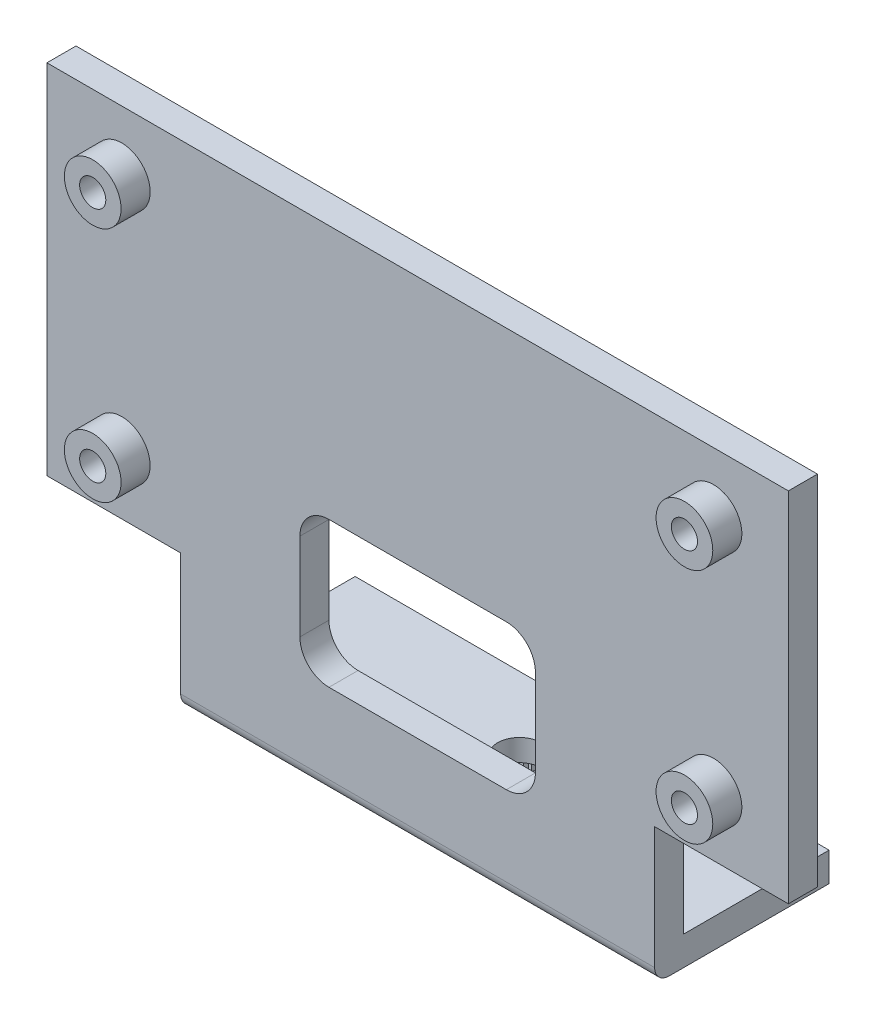
SolidWorks part; units mm, degrees
material "ABS PC"
ref_plane "Front Plane" through (0, 0, 0) normal (0, 0, 1) x (1, 0, 0)
ref_plane "Top Plane" through (0, 0, 0) normal (0, 1, 0) x (1, 0, 0)
ref_plane "Right Plane" through (0, 0, 0) normal (1, 0, 0) x (0, 0, -1)
sketch "Sketch1" plane through (0, 0, 0) normal (0, 1, 0) x (1, 0, 0)
  line L1 (-25.5, 0) -> (25.5, 0)
  line L2 (-25.5, 0) -> (-25.5, 12)
  line L3 (-25.5, 12) -> (25.5, 12)
  line L4 (25.5, 0) -> (25.5, 12)
  point P4 (0, 0)
  dimension "D1" = 12
  dimension "D2" = 51
extrude "Bracket Size" add sketch "Sketch1" along normal blind 34
sketch "Sketch2" plane through (0, 0, 0) normal (1, 0, 0) x (0, 0, -1)
  line L0 (7.7, 0) -> (-7.7, 0) construction
  line L1 (12, 34) -> (2, 34)
  line L2 (12, 34) -> (12, 2)
  line L3 (12, 2) -> (2, 2)
  line L4 (2, 34) -> (2, 2)
  line L5 (0, 20.35) -> (0, -20.35) construction
  line L6 (12, 34) -> (0, 34) construction
  dimension "D1" = 2
  dimension "D2" = 2
extrude "Side Profile" cut sketch "Sketch2" against normal through all both and the other way through all
fillet "Fillet1" radius 1 1 edges at (0, 0, 0)
sketch "Sketch3" plane through (0, 0, 0) normal (0, 0, 1) x (1, 0, 0)
  line L1 (25.5, 0) -> (16.3, 0)
  line L2 (25.5, 0) -> (25.5, 9.4)
  line L3 (25.5, 9.4) -> (16.3, 9.4)
  line L4 (16.3, 0) -> (16.3, 9.4)
  line L9 (-25.5, 0) -> (-16.3, 0)
  line L10 (-25.5, 0) -> (-25.5, 9.4)
  line L11 (-25.5, 9.4) -> (-16.3, 9.4)
  line L12 (-16.3, 0) -> (-16.3, 9.4)
  line L13 (0, 0) -> (0, -5.23) construction
  line L14 (-25.5, 34) -> (25.5, 34) construction
  dimension "D1" = 32.6
  dimension "D2" = 24.6
extrude "Base Trim" cut sketch "Sketch3" against normal through all
sketch "Sketch4" plane through (0, 0, 0) normal (0, 0, 1) x (1, 0, 0)
  line L0 (0, -7.7) -> (0, 7.7) construction
  line L1 (-6.1, 16.5) -> (6.1, 16.5)
  line L2 (-8.1, 14.5) -> (-8.1, 8.5)
  line L3 (-6.1, 6.5) -> (6.1, 6.5)
  line L4 (8.1, 14.5) -> (8.1, 8.5)
  line L5 (-25.5, 34) -> (25.5, 34) construction
  arc A0 (6.1, 6.5) -> (8.1, 8.5) centre (6.1, 8.5) ccw
  arc A1 (6.1, 16.5) -> (8.1, 14.5) centre (6.1, 14.5) cw
  arc A2 (-6.1, 16.5) -> (-8.1, 14.5) centre (-6.1, 14.5) ccw
  arc A3 (-8.1, 8.5) -> (-6.1, 6.5) centre (-6.1, 8.5) ccw
  point P4 (0, 6.5)
  dimension "D1" = 2
  dimension "D2" = 10
  dimension "D3" = 16.2
  dimension "D4" = 17.5
extrude "Wire Reilef Hole" cut sketch "Sketch4" against normal through all
sketch "Sketch5" plane through (0, 0, 0) normal (0, 0, 1) x (1, 0, 0)
  line L0 (0, -7.7) -> (0, 7.7) construction
  line L1 (-20.35, 29.85) -> (20.35, 29.85) construction
  line L2 (-20.35, 29.85) -> (-20.35, 13.55) construction
  line L3 (-20.35, 13.55) -> (20.35, 13.55) construction
  line L4 (20.35, 29.85) -> (20.35, 13.55) construction
  line L5 (20.35, 13.55) -> (20.35, 9.4) construction
  line L6 (20.35, 29.85) -> (20.35, 34) construction
  line L7 (25.5, 9.4) -> (16.3, 9.4) construction
  line L8 (-25.5, 34) -> (25.5, 34) construction
  circle A0 centre (-20.35, 29.85) radius 1.95
  point P5 (0, 13.55)
  point P6 (-20.35, 29.85)
  point P7 (-20.35, 13.55)
  point P8 (20.35, 13.55)
  point P9 (20.35, 29.85)
  dimension "D3" = 3.9
  dimension "D1" = 16.3
  dimension "D2" = 40.7
extrude "Spacer" add sketch "Sketch5" along normal blind 2
hole_wizard "M1.6 Clearance Hole1" positions "Sketch6" profile "Sketch7" hole size "M1.6" standard "ANSI Metric" end condition through all
sketch "Sketch6" plane through (0, 0, 2) normal (0, 0, 1) x (1, 0, 0)
  point P0 (-20.35, 29.85)
sketch "Sketch7" plane through (-20.35, 29.85, 2) normal (1, 0, 0) x (0, -1, 0)
  line L0 (0, 0) -> (0, 14)
  line L1 (0, 14) -> (0.9, 14)
  line L2 (0.9, 14) -> (0.9, 0)
  line L5 (0.9, 0) -> (0, 0)
  line L11 (0, -6.35) -> (0, 107.95) construction
  dimension "Thru Hole Dia." = 1.8
  dimension "Thru Hole Depth" = 14
pattern_sketch "Spacer Pattern" of "Spacer", "M1.6 Clearance Hole1" driven by "Sketch5"
sketch "Sketch8" plane through (0, 0, 0) normal (0, 1, 0) x (1, 0, 0)
  line L0 (0, -7.7) -> (0, 7.7) construction
  line L3 (0, 12) -> (0, 2) construction
  circle A0 centre (0, 7) radius 3.4
  point P6 (0, 7)
  dimension "D1" = 6.8
extrude "Servo Spacer" add sketch "Sketch8" against normal blind 3
sketch "Sketch9" plane through (0, -3, 0) normal (0, -1, 0) x (1, 0, 0)
  line L0 (0.3907, -4.7842) -> (0.2179, -4.5095)
  line L1 (0.2179, -4.5095) -> (0, -4.75)
  line L2 (0, -7.7) -> (0, 7.7) construction
  line L3 (0, -7) -> (0.3907, -4.7842)
  line L4 (0, -4.75) -> (0, -7)
  circle A0 centre (0, -7) radius 2.5 construction
  circle A1 centre (0, -7) radius 2.25 construction
  dimension "D1" = 2.5
  dimension "D2" = 2.25
  dimension "D3" = 10
  dimension "D4" = 0.3245
extrude "Spline Tooth" cut sketch "Sketch9" against normal blind 3.5
pattern_circular "Spline" count 36 over 360 about axis through (0, 0, -7) along (0, 1, 0) of "Spline Tooth"
hole_wizard "M2 Clearance Hole1" positions "Sketch10" profile "Sketch11" hole size "M2" standard "ANSI Metric" end condition through all
sketch "Sketch10" plane through (0, 0, 0) normal (0, 1, 0) x (1, 0, 0)
  point P0 (0, 7)
sketch "Sketch11" plane through (0, 0, -7) normal (1, 0, 0) x (0, 0, -1)
  line L0 (0, 0) -> (0, 34)
  line L1 (0, 34) -> (1.5, 34)
  line L2 (1.5, 34) -> (1.5, 0)
  line L5 (1.5, 0) -> (0, 0)
  line L11 (0, -6.35) -> (0, 107.95) construction
  dimension "Thru Hole Dia." = 3
  dimension "Thru Hole Depth" = 34
